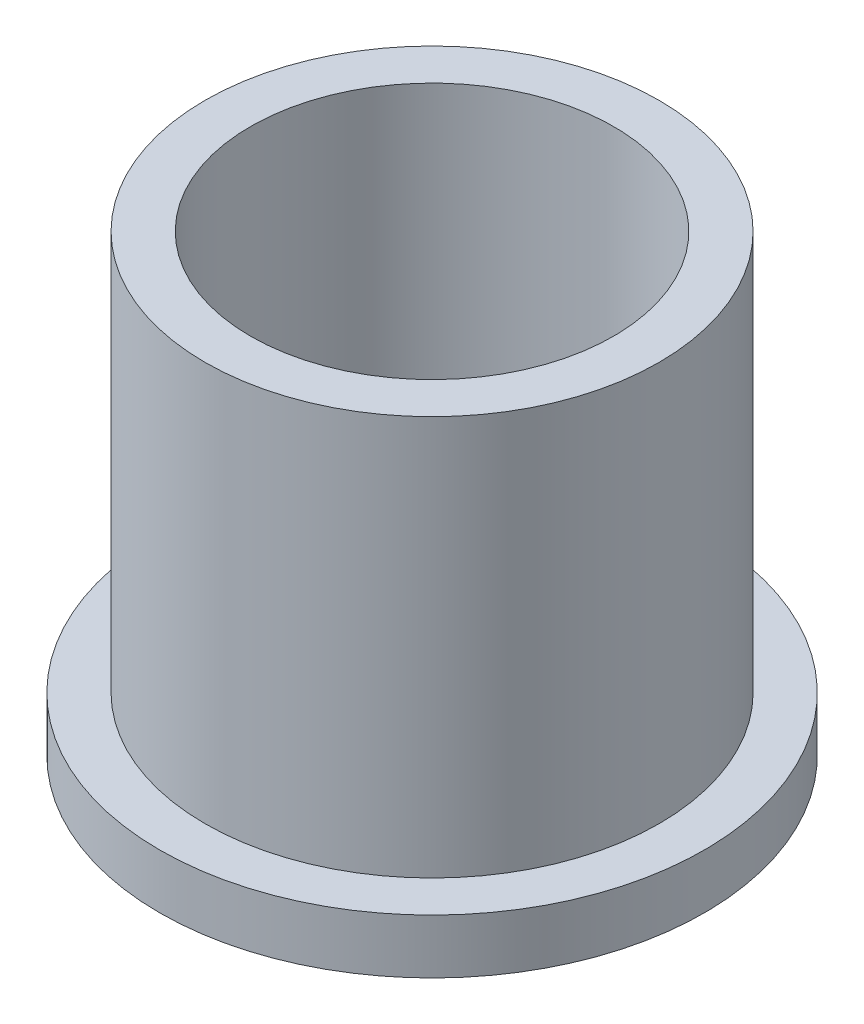
SolidWorks part; units mm, degrees
ref_plane "정면" through (0, 0, 0) normal (0, 0, 1) x (1, 0, 0)
ref_plane "윗면" through (0, 0, 0) normal (0, 1, 0) x (1, 0, 0)
ref_plane "우측면" through (0, 0, 0) normal (1, 0, 0) x (0, 0, -1)
sketch "스케치1" plane through (0, 0, 0) normal (0, 0, 1) x (1, 0, 0)
  line L0 (10, 25) -> (12.5, 25)
  line L1 (12.5, 25) -> (12.5, 3)
  line L2 (12.5, 3) -> (15, 3)
  line L3 (15, 3) -> (15, 0)
  line L4 (15, 0) -> (10, 0)
  line L5 (10, 0) -> (10, 25)
  line L6 (0, 34.5626) -> (0, -29.5194) construction
  dimension "D1" = 3
  dimension "D2" = 2.5
  dimension "D3" = 25
  dimension "D4" = 2.5
  dimension "D5" = 10
revolve "회전1" add sketch "스케치1" angle 360 about L6
